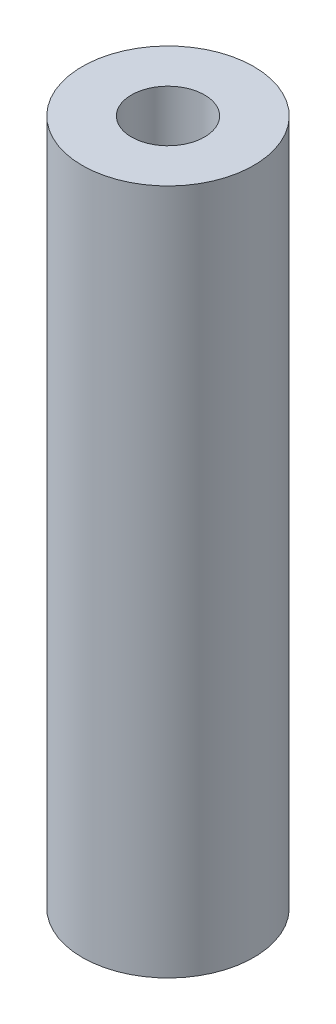
SolidWorks part; units mm, degrees
ref_plane "Front Plane" through (0, 0, 0) normal (0, 0, 1) x (1, 0, 0)
ref_plane "Top Plane" through (0, 0, 0) normal (0, 1, 0) x (1, 0, 0)
ref_plane "Right Plane" through (0, 0, 0) normal (1, 0, 0) x (0, 0, -1)
sketch "Sketch1" plane through (0, 0, 0) normal (0, 1, 0) x (1, 0, 0)
  circle A0 centre (0, 0) radius 3.175
  dimension "D1" = 6.35
extrude "Boss-Extrude1" add sketch "Sketch1" along normal blind 25.4
hole_wizard "Tap Drill for #6-32 Tap1" positions "Sketch3" profile "Sketch2" hole size "#6-32" standard "ANSI Inch" end condition through all
sketch "Sketch3" plane through (0, 25.4, 0) normal (0, 1, 0) x (1, 0, 0)
  point P0 (0, 0)
sketch "Sketch2" plane through (0, 25.4, 0) normal (1, 0, 0) x (0, 0, 1)
  line L0 (0, 0) -> (0, 25.4)
  line L1 (0, 25.4) -> (1.3525, 25.4)
  line L2 (1.3525, 25.4) -> (1.3525, 0)
  line L5 (1.3525, 0) -> (0, 0)
  line L11 (0, -6.35) -> (0, 107.95) construction
  dimension "Thru Hole Dia." = 2.7051
  dimension "Thru Hole Depth" = 25.4
